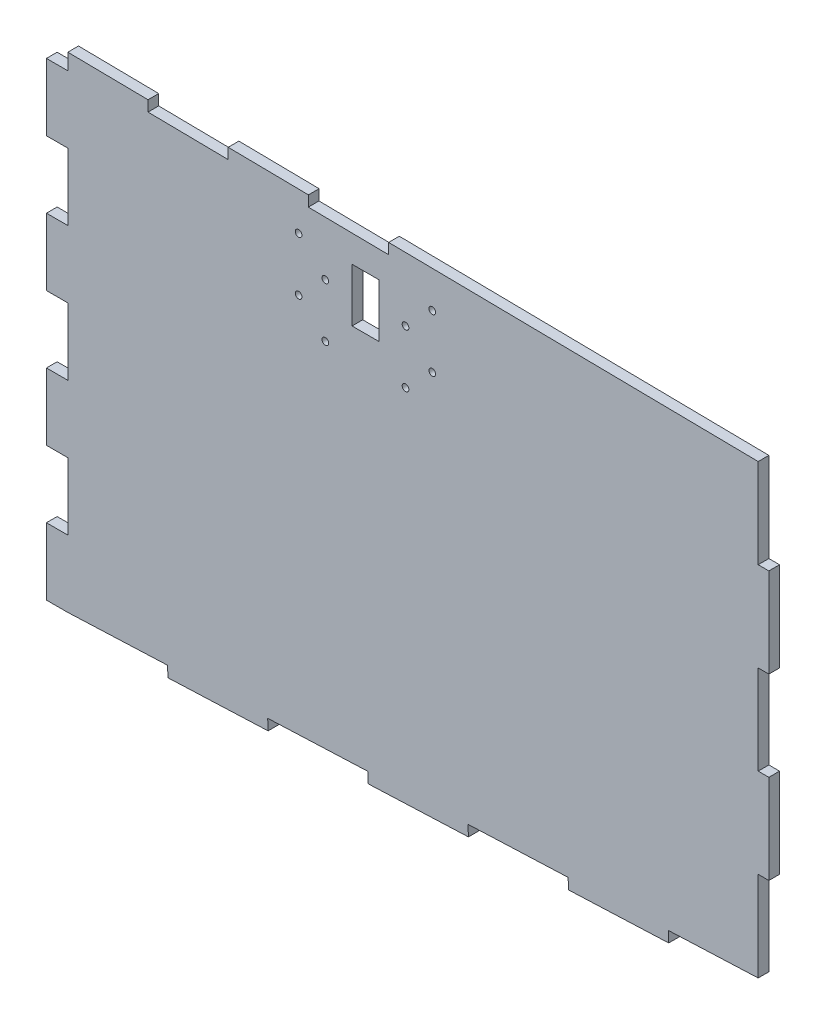
SolidWorks part; units mm, degrees
material "A-Glass Fiber"
ref_plane "Front Plane" through (0, 0, 0) normal (0, 0, 1) x (1, 0, 0)
ref_plane "Top Plane" through (0, 0, 0) normal (0, 1, 0) x (1, 0, 0)
ref_plane "Right Plane" through (0, 0, 0) normal (1, 0, 0) x (0, 0, -1)
sketch "Sketch1" plane through (0, 0, 0) normal (0, 0, 1) x (1, 0, 0)
  line L0 (20.32, 10.1649) -> (781.2461, 41.6972)
  line L1 (781.2461, 41.6972) -> (781.6666, 31.5497)
  line L2 (686.4983, 27.606) -> (781.6666, 31.5497)
  line L3 (20.32, 10.1649) -> (20.32, 328.5902)
  line L4 (20.32, 328.5902) -> (20.269, 455.9603)
  line L5 (20.32, 328.5902) -> (0, 328.5902)
  line L6 (20.32, 328.5902) -> (20.32, 10.1649)
  line L9 (781.2461, 41.6972) -> (778.0911, 117.8318)
  line L11 (20.32, 0) -> (115.4883, 3.9437)
  line L12 (0, 328.5902) -> (20.32, 328.5902)
  line L13 (0, 328.5902) -> (0, 264.9051)
  line L14 (0, 264.9051) -> (20.32, 264.9051)
  line L15 (20.32, 328.5902) -> (20.32, 264.9051)
  line L16 (20.32, 264.9051) -> (0, 264.9051)
  line L17 (20.32, 264.9051) -> (20.32, 201.2201)
  line L18 (20.32, 201.2201) -> (0, 201.2201)
  line L19 (0, 264.9051) -> (0, 201.2201)
  line L20 (0, 201.2201) -> (20.32, 201.2201)
  line L21 (0, 201.2201) -> (0, 137.535)
  line L22 (0, 137.535) -> (20.32, 137.535)
  line L23 (20.32, 201.2201) -> (20.32, 137.535)
  line L24 (20.32, 137.535) -> (0, 137.535)
  line L25 (20.32, 137.535) -> (20.32, 73.85)
  line L26 (20.32, 73.85) -> (0, 73.85)
  line L27 (0, 137.535) -> (0, 73.85)
  line L28 (0, 73.85) -> (20.32, 73.85)
  line L29 (0, 73.85) -> (0, 10.1649)
  line L31 (20.32, 73.85) -> (20.32, 0)
  line L33 (115.4883, 3.9437) -> (115.0678, 14.0912)
  line L34 (20.32, 10.1649) -> (115.0678, 14.0912)
  line L35 (115.4883, 3.9437) -> (115.0678, 14.0912)
  line L36 (115.4883, 3.9437) -> (210.6566, 7.8874)
  line L37 (115.0678, 14.0912) -> (210.2361, 18.0349)
  line L38 (210.6566, 7.8874) -> (210.2361, 18.0349)
  line L39 (210.2361, 18.0349) -> (210.6566, 7.8874)
  line L40 (210.2361, 18.0349) -> (305.4045, 21.9786)
  line L41 (210.6566, 7.8874) -> (305.825, 11.8311)
  line L42 (305.4045, 21.9786) -> (305.825, 11.8311)
  line L43 (305.4045, 21.9786) -> (305.825, 11.8311)
  line L44 (305.4045, 21.9786) -> (400.5728, 25.9223)
  line L45 (305.825, 11.8311) -> (400.9933, 15.7748)
  line L46 (400.5728, 25.9223) -> (400.9933, 15.7748)
  line L47 (400.9933, 15.7748) -> (400.5728, 25.9223)
  line L48 (400.9933, 15.7748) -> (496.1616, 19.7186)
  line L49 (400.5728, 25.9223) -> (495.7411, 29.866)
  line L50 (496.1616, 19.7186) -> (495.7411, 29.866)
  line L51 (495.7411, 29.866) -> (496.1616, 19.7186)
  line L52 (495.7411, 29.866) -> (590.9094, 33.8097)
  line L53 (496.1616, 19.7186) -> (591.3299, 23.6623)
  line L54 (590.9094, 33.8097) -> (591.3299, 23.6623)
  line L55 (590.9094, 33.8097) -> (591.3299, 23.6623)
  line L56 (590.9094, 33.8097) -> (686.0778, 37.7535)
  line L57 (591.3299, 23.6623) -> (686.4983, 27.606)
  line L58 (686.0778, 37.7535) -> (686.4983, 27.606)
  line L59 (20.32, 10.1649) -> (0, 10.1649)
  line L60 (20.32, 10.1649) -> (20.32, 0)
  line L61 (20.32, 0) -> (0, 0) construction
  line L62 (0, 0) -> (0, 10.1649) construction
  line L63 (781.2461, 41.6972) -> (781.2461, 471.9516)
  line L64 (20.32, 328.5902) -> (0, 328.5902)
  line L65 (20.32, 328.5902) -> (20.32, 392.2753)
  line L66 (0, 328.5902) -> (0, 392.2753)
  line L67 (20.32, 392.2753) -> (0, 392.2753)
  line L68 (20.32, 392.2753) -> (0, 392.2753)
  line L69 (20.32, 392.2753) -> (20.32, 455.9603)
  line L70 (0, 392.2753) -> (0, 455.9603)
  line L71 (20.32, 455.9603) -> (0, 455.9603)
  line L72 (20.32, 455.9603) -> (0, 455.9603)
  line L73 (20.32, 455.9603) -> (20.32, 519.6454)
  line L74 (0, 455.9603) -> (0, 519.6454)
  line L75 (20.32, 519.6454) -> (0, 519.6454)
  line L76 (20.32, 328.5902) -> (20.32, 519.6454)
  arc A0 (1445.699, 402.1929) -> (-664.1875, 533.4087) centre (-664.1875, -16495.1746) ccw construction
  arc A1 (25.4125, 0.0087) -> (1875.8125, 190.5087) centre (25.4125, 9082.0833) ccw construction
  arc A2 (781.2461, 471.9516) -> (20.32, 519.6454) centre (-664.1875, -16495.1746) ccw
  dimension "D1" = 762
  dimension "D4" = 76.2
  dimension "D5" = 20.32
  dimension "D7" = 10.1562
extrude "Boss-Extrude1" add sketch "Sketch1" along normal blind 10.16
sketch "Sketch2" plane through (0, 0, 10.16) normal (0, 0, 1) x (1, 0, 0)
  line L0 (20.32, 471.239) -> (781.2461, 460.9484)
  line L1 (20.32, 455.9603) -> (20.32, 519.6454) construction
  line L2 (781.2461, 41.6972) -> (781.2461, 471.9516) construction
  line L3 (20.32, 471.239) -> (20.32, 535.0179)
  line L4 (20.32, 535.0179) -> (781.2461, 535.0179)
  line L5 (781.2461, 535.0179) -> (781.2461, 460.9484)
  point P6 (116.1565, 0)
  dimension "D1" = 469.9
extrude "Cut-Extrude1" cut sketch "Sketch2" against normal through all
sketch "Sketch3" plane through (0, 0, 0) normal (0, 0, -1) x (-1, 0, 0)
  line L2 (-20.32, 471.239) -> (-781.2461, 460.9484) construction
  line L3 (-96.52, 470.2085) -> (-20.32, 471.239)
sketch "Sketch4" plane through (0, 0, 0) normal (0, 0, -1) x (-1, 0, 0)
  line L1 (-686.4983, 27.606) -> (-816.0458, 27.606)
  line L2 (-686.4983, 27.606) -> (-686.4983, 471.6431)
  line L3 (-686.4983, 471.6431) -> (-816.0458, 471.6431)
  line L4 (-816.0458, 27.606) -> (-816.0458, 471.6431)
extrude "Cut-Extrude3" cut sketch "Sketch4" against normal through all
sketch "Sketch5" plane through (0, 0, 0) normal (0, 0, -1) x (-1, 0, 0)
  line L0 (-686.4983, 27.606) -> (-686.4983, 462.2297) construction
  line L1 (-686.4983, 37.7535) -> (-676.3383, 37.7535)
  line L2 (-686.4983, 37.7535) -> (-686.4983, 122.6762)
  line L3 (-686.4983, 122.6762) -> (-676.3383, 122.6762)
  line L4 (-676.3383, 37.7535) -> (-676.3383, 122.6762)
  line L5 (-20.32, 471.239) -> (-686.4983, 462.2297) construction
  line L6 (-686.4983, 122.6762) -> (-676.3383, 122.6762)
  line L7 (-686.4983, 122.6762) -> (-686.4983, 207.5989)
  line L8 (-686.4983, 207.5989) -> (-676.3383, 207.5989)
  line L9 (-676.3383, 122.6762) -> (-676.3383, 207.5989)
  line L10 (-686.4983, 207.5989) -> (-676.3383, 207.5989)
  line L11 (-686.4983, 207.5989) -> (-686.4983, 292.5217)
  line L12 (-686.4983, 292.5217) -> (-676.3383, 292.5217)
  line L13 (-676.3383, 207.5989) -> (-676.3383, 292.5217)
  line L14 (-686.4983, 292.5217) -> (-676.3383, 292.5217)
  line L15 (-686.4983, 292.5217) -> (-686.4983, 377.4444)
  line L16 (-686.4983, 377.4444) -> (-676.3383, 377.4444)
  line L17 (-676.3383, 292.5217) -> (-676.3383, 377.4444)
  line L18 (-686.4983, 377.4444) -> (-676.3383, 377.4444)
  line L19 (-686.4983, 377.4444) -> (-686.4983, 462.3671)
  line L20 (-686.4983, 462.3671) -> (-676.3383, 462.3671)
  line L21 (-676.3383, 377.4444) -> (-676.3383, 462.3671)
  line L23 (-686.4983, 37.7535) -> (-676.3383, 37.7535)
  line L24 (-686.4983, 37.7535) -> (-686.4983, 26.1578)
  line L25 (-686.4983, 26.1578) -> (-676.3383, 26.1578)
  line L26 (-676.3383, 37.7535) -> (-676.3383, 26.1578)
  line M9 (-20.32, 471.239) -> (-686.4983, 462.2297)
  line M10 (-686.4983, 462.2297) -> (-686.4983, 27.606)
  line M11 (-686.4983, 27.606) -> (-686.0778, 37.7535)
  line M12 (-686.0778, 37.7535) -> (-590.9094, 33.8097)
  dimension "D1" = 10.16
extrude "Cut-Extrude5" cut sketch "Sketch5" against normal through all contours L1 L4 L3 M10 | L8 L13 L12 M10 | L16 L21 M9 M10 | L26 L24 L25 M12 M11 | L1 M10 M11 | L26 L1 M12
sketch "Sketch9" plane through (0, 0, 0) normal (0, 0, -1) x (-1, 0, 0)
  line L4 (-248.8374, 457.9915) -> (-248.9748, 468.1506)
  line L5 (-325.0304, 456.9611) -> (-248.8374, 457.9915)
  line L6 (-325.1678, 467.1202) -> (-248.9748, 468.1506)
  line L7 (-325.0304, 456.9611) -> (-325.1678, 467.1202)
  line L9 (-20.32, 455.9603) -> (-20.32, 471.239) construction
  line L11 (-20.32, 455.9603) -> (-20.32, 471.239)
  line L14 (-96.52, 470.2085) -> (-96.52, 460.0485)
  line L15 (-96.52, 460.0485) -> (-172.713, 459.0181)
  line L16 (-172.713, 459.0181) -> (-172.713, 469.1781)
  line L17 (-172.713, 469.1781) -> (-96.52, 470.2085)
  point P3 (-20.32, 471.239)
  point P13 (-20.32, 463.5997)
  point P16 (-172.713, 464.0981)
  dimension "D1" = 76.2
  dimension "D2" = 76.2
  dimension "D3" = 10.16
  dimension "D4" = 76.2
  dimension "D5" = 76.193
  dimension "D6" = 10.1591
extrude "Cut-Extrude6" cut sketch "Sketch9" against normal through all
sketch "Sketch10" plane through (0, 0, 10.16) normal (0, 0, 1) x (1, 0, 0)
  line L0 (676.3383, 452.21) -> (20.32, 461.0819)
  line L1 (676.3383, 377.4444) -> (676.3383, 462.3671) construction
  line L2 (325.0304, 456.9611) -> (248.8374, 457.9915) construction
  line L4 (20.32, 461.0819) -> (20.32, 10.1649)
  line L5 (20.32, 10.1649) -> (676.3383, 37.3499)
  line L6 (676.3383, 37.3499) -> (676.3383, 452.21)
  line L7 (71.12, 409.5903) -> (71.12, 63.1136)
  line L8 (71.12, 63.1136) -> (625.5383, 86.0883)
  line L9 (625.5383, 86.0883) -> (625.5383, 402.0924)
  line L10 (625.5383, 402.0924) -> (71.12, 409.5903)
  line L11 (71.12, 409.5903) -> (625.5383, 86.0883)
  line L12 (625.5383, 402.0924) -> (71.12, 63.1136)
  line L13 (589.809, 402.5756) -> (71.12, 85.4422)
  line L14 (71.12, 387.5345) -> (590.2454, 84.6258)
  line L15 (625.5383, 379.7638) -> (110.2947, 64.737)
  line L16 (109.8162, 409.067) -> (625.5383, 108.1442)
  line L17 (615.6011, 418.3452) -> (61.1828, 79.3664) construction
  line L18 (61.5192, 393.1365) -> (615.9375, 69.6345) construction
  line L19 (80.7208, 426.0441) -> (635.139, 102.5421) construction
  line L20 (635.4755, 385.8396) -> (81.0572, 46.8608) construction
  dimension "D1" = 50.8
  dimension "D2" = 19.05
  dimension "D3" = 19.05
sketch "Sketch11" plane through (0, 0, 10.16) normal (0, 0, 1) x (1, 0, 0)
  line L0 (315.8194, 431.7708) -> (290.4194, 380.9708) construction
  line L1 (303.1194, 406.3708) -> (303.1194, 190.5708) construction
  line L2 (239.6194, 406.3708) -> (265.0194, 406.3708) construction
  line L3 (226.9194, 368.2708) -> (379.3194, 368.2708) construction
  line L4 (315.8194, 431.7708) -> (290.4194, 431.7708)
  line L5 (290.4194, 431.7708) -> (290.4194, 380.9708)
  line L6 (290.4194, 380.9708) -> (315.8194, 380.9708)
  line L7 (315.8194, 380.9708) -> (315.8194, 431.7708)
  line L8 (315.8194, 431.7708) -> (290.4194, 431.7708)
  line L9 (290.4194, 431.7708) -> (290.4194, 380.9708)
  line L10 (290.4194, 380.9708) -> (315.8194, 380.9708)
  line L11 (315.8194, 380.9708) -> (315.8194, 431.7708)
  line L12 (226.9194, 368.2708) -> (226.9194, 444.4708) construction
  line L13 (226.9194, 444.4708) -> (379.3194, 444.4708) construction
  line L14 (379.3194, 368.2708) -> (379.3194, 444.4708) construction
  line L15 (226.9194, 368.2708) -> (379.3194, 444.4708) construction
  line L16 (226.9194, 444.4708) -> (379.3194, 368.2708) construction
  line L17 (239.6194, 380.9708) -> (366.6194, 380.9708) construction
  line L18 (239.6194, 380.9708) -> (239.6194, 431.7708) construction
  line L19 (239.6194, 431.7708) -> (366.6194, 431.7708) construction
  line L20 (366.6194, 380.9708) -> (366.6194, 431.7708) construction
  line L21 (239.6194, 380.9708) -> (366.6194, 431.7708) construction
  line L22 (239.6194, 431.7708) -> (366.6194, 380.9708) construction
  circle A0 centre (366.6194, 431.7708) radius 3.175
  circle A1 centre (303.1194, 190.5708) radius 165
  circle A2 centre (303.1194, 190.5708) radius 165 construction
  circle A3 centre (366.6194, 380.9708) radius 3.175
  circle A4 centre (239.6194, 431.7708) radius 3.175
  circle A5 centre (239.6194, 380.9708) radius 3.175
  circle A6 centre (265.0194, 406.3708) radius 3.175
  circle A7 centre (341.2194, 406.3708) radius 3.175
  circle A8 centre (265.0194, 355.5708) radius 3.175
  circle A9 centre (341.2194, 355.5708) radius 3.175
  dimension "D7" = 25.4
  dimension "D8" = 6.35
  dimension "D9" = 50.8
  dimension "D3" = 76.2
  dimension "D4" = 152.4
  dimension "D5" = 50.8
  dimension "D6" = 127
  dimension "D10" = 25.4
  dimension "D1" = 0
  dimension "D2" = 0
extrude "Cut-Extrude8" cut sketch "Sketch11" against normal through all
